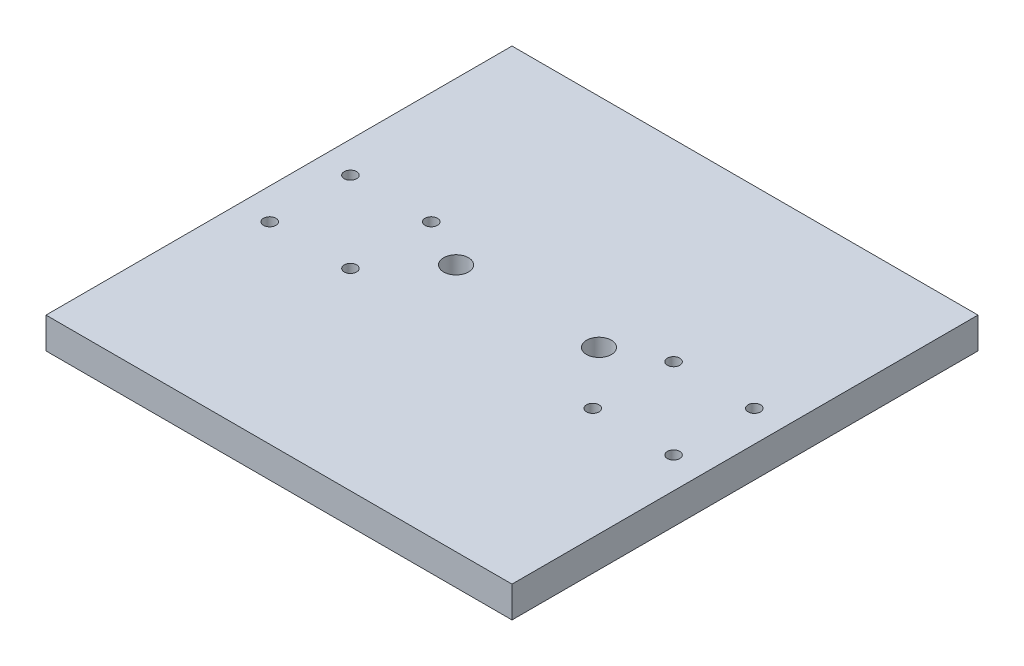
SolidWorks part; units mm, degrees
ref_plane "Front Plane" through (0, 0, 0) normal (0, 0, 1) x (1, 0, 0)
ref_plane "Top Plane" through (0, 0, 0) normal (0, 1, 0) x (1, 0, 0)
ref_plane "Right Plane" through (0, 0, 0) normal (1, 0, 0) x (0, 0, -1)
sketch "Sketch1" plane through (0, 0, 0) normal (0, 1, 0) x (1, 0, 0)
  line L1 (-75, 75) -> (75, 75)
  line L2 (-75, 75) -> (-75, -75)
  line L3 (-75, -75) -> (75, -75)
  line L4 (75, 75) -> (75, -75)
  line L5 (-75, 75) -> (75, -75) construction
  line L6 (-75, -75) -> (75, 75) construction
  point P0 (0, 0)
  dimension "D1" = 150
  dimension "D2" = 150
extrude "Boss-Extrude1" add sketch "Sketch1" along normal blind 10
sketch "Sketch2" plane through (0, 10, 0) normal (0, 1, 0) x (1, 0, 0)
  line L4 (75, 75) -> (-75, 75) construction
  line L6 (0, 75) -> (0, -75) construction
  line L7 (-75, -75) -> (75, -75) construction
  circle A4 centre (23, 5) radius 4
  circle A9 centre (-23, 5) radius 4
  circle A10 centre (-65, 13) radius 2
  circle A11 centre (-39, 13) radius 2
  circle A12 centre (-65, -13) radius 2
  circle A13 centre (-39, -13) radius 2
  circle A14 centre (39, 13) radius 2
  circle A15 centre (65, 13) radius 2
  circle A16 centre (65, -13) radius 2
  circle A17 centre (39, -13) radius 2
  point P18 (0, 0)
  dimension "D8" = 8
  dimension "D1" = 4
  dimension "D2" = 26
  dimension "D3" = 26
  dimension "D4" = 16
  dimension "D6" = 23
  dimension "D7" = 70
extrude "Cut-Extrude1" cut sketch "Sketch2" against normal blind 10
